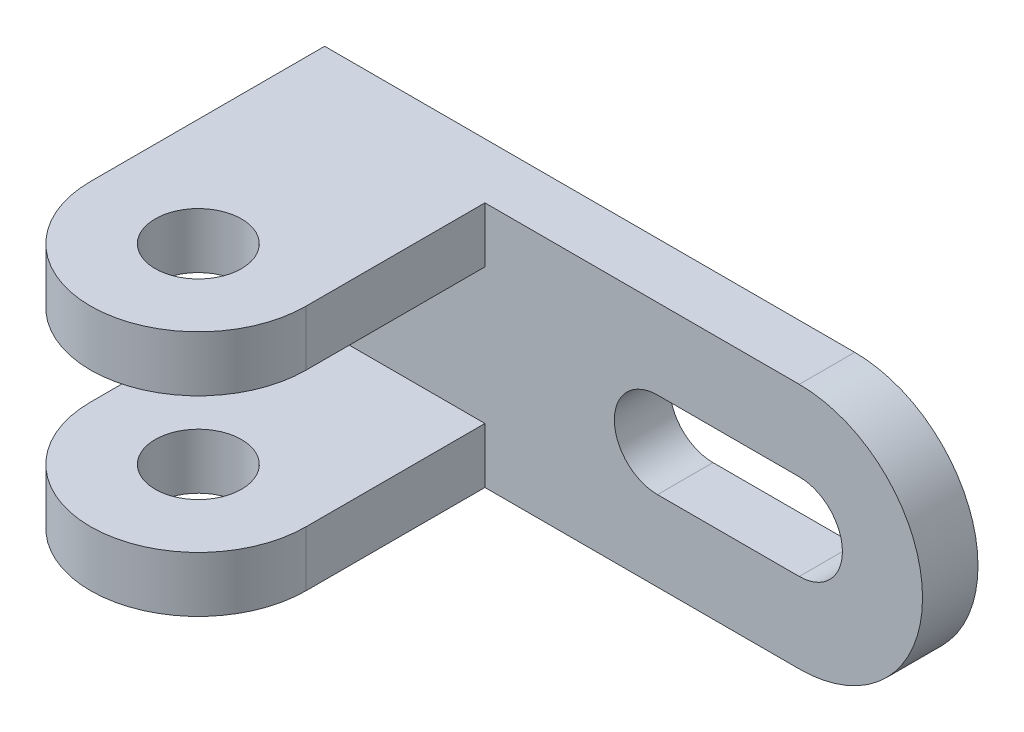
SolidWorks part; units mm, degrees
ref_plane "Front Plane" through (0, 0, 0) normal (0, 0, 1) x (1, 0, 0)
ref_plane "Top Plane" through (0, 0, 0) normal (0, 1, 0) x (1, 0, 0)
ref_plane "Right Plane" through (0, 0, 0) normal (1, 0, 0) x (0, 0, -1)
sketch "Sketch1" plane through (0, 0, 0) normal (0, 0, 1) x (1, 0, 0)
  line L0 (0, 0) -> (86, 0) construction
  line L1 (0, -20) -> (86, -20)
  line L2 (0, -20) -> (0, 20)
  line L3 (0, 20) -> (86, 20)
  line L5 (63, 0) -> (86, 0) construction
  line L6 (63, 7) -> (86, 7)
  line L7 (63, -7) -> (86, -7)
  arc A0 (86, -20) -> (86, 20) centre (86, 0) ccw
  arc A1 (63, 7) -> (63, -7) centre (63, 0) ccw
  arc A2 (86, -7) -> (86, 7) centre (86, 0) ccw
  point P0 (0, 0)
  point P6 (74.5, 0)
  point P14 (0, 0)
  dimension "D3" = 23
  dimension "D4" = 14
  dimension "D1" = 86
  dimension "D2" = 40
extrude "Boss-Extrude1" add sketch "Sketch1" along normal blind 9
sketch "Sketch3" plane through (0, -20, 0) normal (0, -1, 0) x (1, 0, 0)
  line L1 (0, 0) -> (35, 0)
  line L2 (0, 0) -> (0, 38)
  line L4 (35, 0) -> (35, 38)
  circle A0 centre (17.5, 38) radius 17.5
  circle A1 centre (17.5, 38) radius 7
  line M5 (0, 0) -> (86, 0)
  line M7 (86, 9) -> (0, 9)
  line M8 (0, 9) -> (0, 0)
  dimension "D1" = 35
  dimension "D2" = 14
  dimension "D3" = 38
extrude "Boss-Extrude2" add sketch "Sketch3" against normal blind 9 contours A0 L2 L4 M7 | A0 A1 | L4 M5 M7 M8
mirror "Mirror1" about plane through (0, 0, 0) normal (0, 1, 0) of "Boss-Extrude2"
